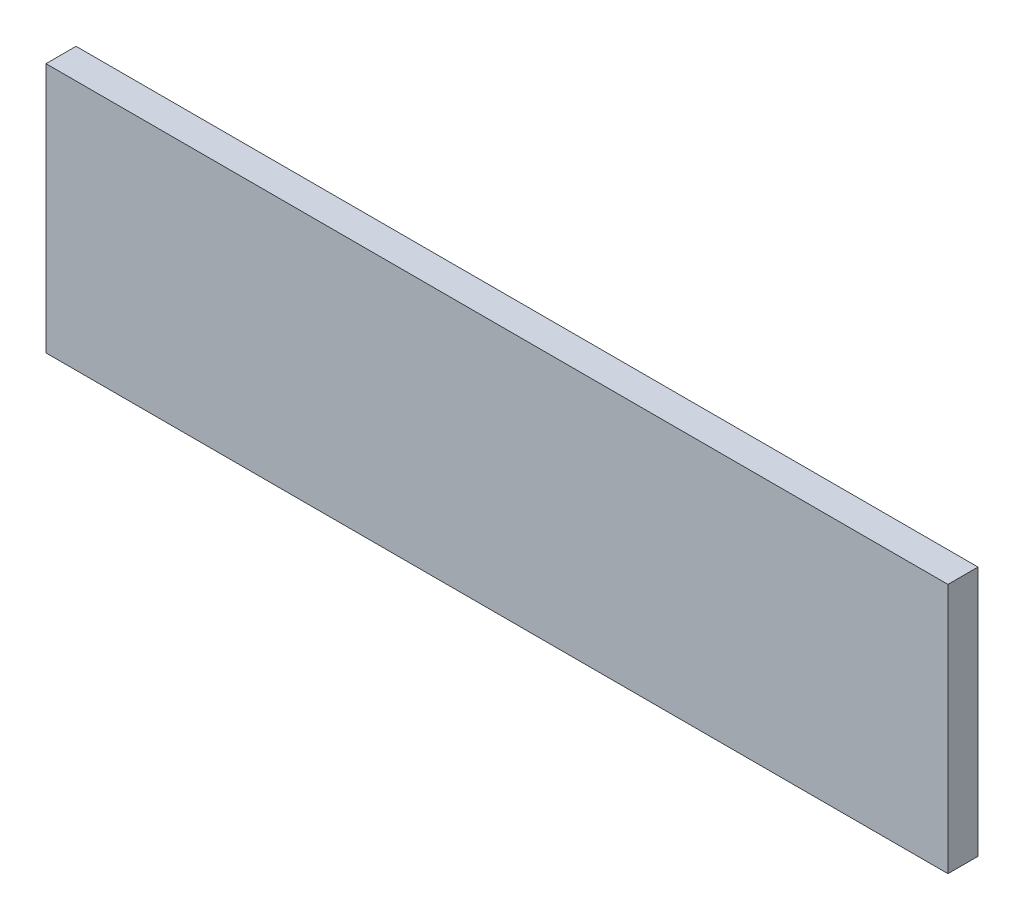
SolidWorks part; units mm, degrees
ref_plane "Plan de face" through (0, 0, 0) normal (0, 0, 1) x (1, 0, 0)
ref_plane "Plan de dessus" through (0, 0, 0) normal (0, 1, 0) x (1, 0, 0)
ref_plane "Plan de droite" through (0, 0, 0) normal (1, 0, 0) x (0, 0, -1)
sketch "Esquisse1" plane through (0, 0, 0) normal (0, 0, 1) x (1, 0, 0)
  line L1 (-45, 12.5) -> (45, 12.5)
  line L2 (-45, 12.5) -> (-45, -12.5)
  line L3 (-45, -12.5) -> (45, -12.5)
  line L4 (45, 12.5) -> (45, -12.5)
  line L5 (-45, 12.5) -> (45, -12.5) construction
  line L6 (-45, -12.5) -> (45, 12.5) construction
  point P0 (0, 0)
  dimension "D1" = 25
  dimension "D2" = 90
extrude "Boss.-Extru.1" add sketch "Esquisse1" along normal blind 3
